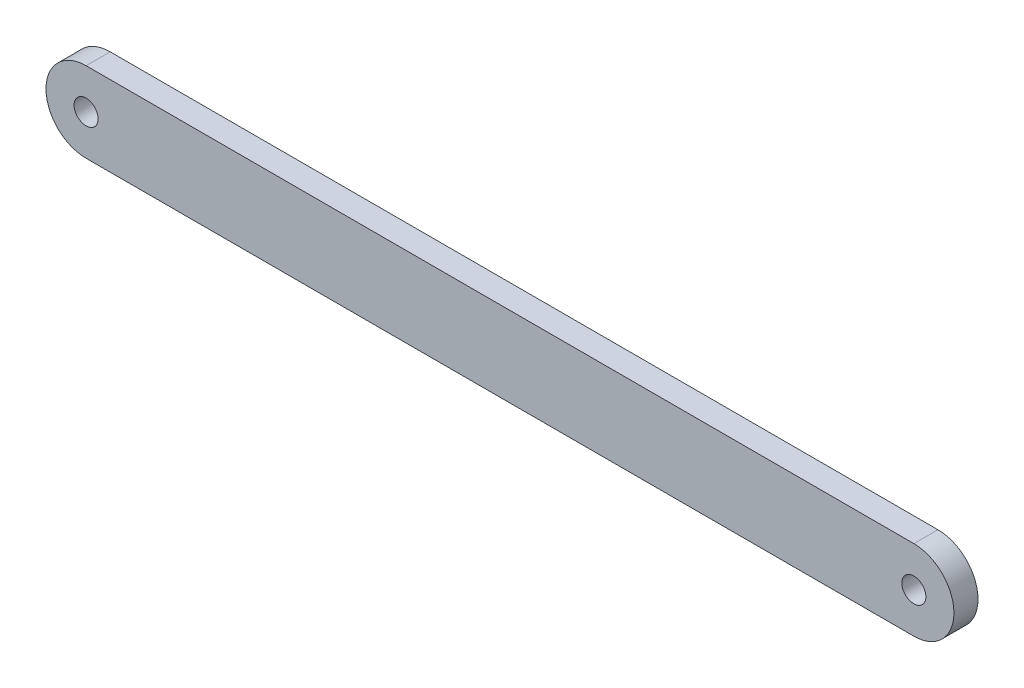
SolidWorks part; units mm, degrees
ref_plane "前基準面" through (0, 0, 0) normal (0, 0, 1) x (1, 0, 0)
ref_plane "上基準面" through (0, 0, 0) normal (0, 1, 0) x (1, 0, 0)
ref_plane "右基準面" through (0, 0, 0) normal (1, 0, 0) x (0, 0, -1)
sketch "草圖1" plane through (0, 0, 0) normal (0, 0, 1) x (1, 0, 0)
  line L0 (-25.805, 0) -> (25.805, 0) construction
  line L1 (-25.805, 2.5) -> (25.805, 2.5)
  line L2 (-25.805, -2.5) -> (25.805, -2.5)
  arc A0 (-25.805, 2.5) -> (-25.805, -2.5) centre (-25.805, 0) ccw
  arc A1 (25.805, -2.5) -> (25.805, 2.5) centre (25.805, 0) ccw
  circle A2 centre (25.805, 0) radius 0.75
  circle A3 centre (-25.805, 0) radius 0.75
  point P3 (0, 0)
  dimension "D2" = 2.5
  dimension "D3" = 1.5
  dimension "D1" = 51.61
extrude "填料-伸長1" add sketch "草圖1" along normal mid plane 1.5
